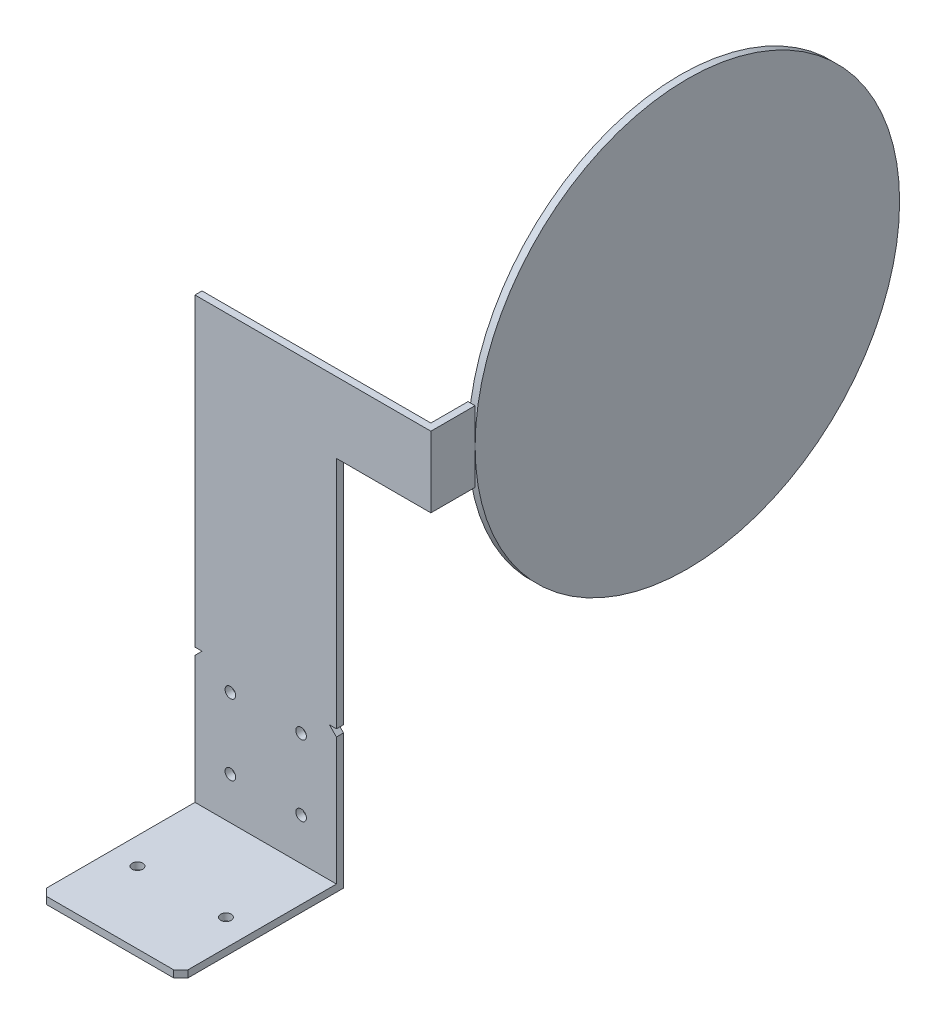
SolidWorks part; units mm, degrees
other "Markup1"
sketch "Sketch7" plane through (0, -72, -122) normal (-0.0435, -0.7938, -0.6066) x (-0.1684, -0.5927, 0.7876)
other "Markup2"
sketch "Sketch8" plane through (0, -72, -122) normal (-0.0435, -0.7938, -0.6066) x (-0.1684, -0.5927, 0.7876)
ref_plane "Спереди" through (0, 0, 0) normal (0, 0, 1) x (1, 0, 0)
ref_plane "Сверху" through (0, 0, 0) normal (0, 1, 0) x (1, 0, 0)
ref_plane "Справа" through (0, 0, 0) normal (1, 0, 0) x (0, 0, -1)
sketch "Sketch1" plane through (0, 0, 0) normal (1, 0, 0) x (0, 0, -1)
  line L0 (0, 0) -> (0, 38)
  line L1 (0, 38) -> (2, 38)
  line L2 (2, 38) -> (2, -2)
  line L3 (2, -2) -> (-44, -2)
  line L4 (-44, -2) -> (-44, 0)
  line L5 (-44, 0) -> (0, 0)
  dimension "D1" = 2
  dimension "D2" = 2
  dimension "D3" = 46
  dimension "D4" = 40
extrude "Extrude1" add sketch "Sketch1" along normal blind 40
sketch "Sketch2" plane through (0, -2, 0) normal (0, -1, 0) x (-1, 0, 0)
  line L0 (-40, 2) -> (0, 2) construction
  line L1 (-7.5, -23.75) -> (-32.5, -23.75) construction
  line L2 (-40, -44) -> (0, -44) construction
  circle A0 centre (-32.5, -23.75) radius 1.5
  circle A1 centre (-7.5, -23.75) radius 1.5
  point P5 (-20, -23.75)
  point P10 (-20, -44)
  dimension "D1" = 3
  dimension "D2" = 25
  dimension "D3" = 25.75
extrude "Extrude2" cut sketch "Sketch2" against normal up to next contours A0
sketch "Sketch3" plane through (0, 0, -2) normal (0, 0, -1) x (-1, 0, 0)
  line L1 (0, -2) -> (0, 38) construction
  line L2 (-40, 38) -> (0, 38) construction
  circle A0 centre (-10, 31.9) radius 1.5
  circle A1 centre (-30, 31.9) radius 1.5
  circle A2 centre (-30, 11.9) radius 1.5
  circle A3 centre (-10, 11.9) radius 1.5
  dimension "D1" = 10
  dimension "D2" = 6.1
  dimension "D3" = 2
  dimension "D4" = 2
extrude "Extrude3" cut sketch "Sketch3" against normal up to next
chamfer "Chamfer1" distance 2 angle 45 4 edges at (40, -1, 44) (0, -1, 44) (0, 38, -1) (40, 38, -1)
sketch "Sketch9" plane through (0, 0, -2) normal (0, 0, -1) x (-1, 0, 0)
  line L0 (-38, 38) -> (-2, 38) construction
  line L1 (0, 38) -> (-40, 38)
  line L2 (0, 38) -> (0, 124.21)
  line L3 (0, 124.21) -> (-40, 124.21)
  line L4 (-40, 38) -> (-40, 124.21)
  line L5 (-40, -2) -> (-40, 36) construction
  line L6 (0, -2) -> (0, 36) construction
  line L7 (-30, 31.9) -> (-10, 11.9) construction
  line L8 (-10, 31.9) -> (-30, 11.9) construction
  point P18 (-20, 21.9)
  dimension "D1" = 102.31
extrude "Boss-Extrude1" add sketch "Sketch9" against normal blind 2
sketch "Sketch11" plane through (0, 0, -2) normal (0, 0, -1) x (-1, 0, 0)
  line L1 (-40, 124.21) -> (-66.69, 124.21)
  line L2 (-40, 124.21) -> (-40, 104.21)
  line L3 (-40, 104.21) -> (-66.69, 104.21)
  line L4 (-66.69, 124.21) -> (-66.69, 104.21)
  dimension "D1" = 26.69
  dimension "D2" = 20
extrude "Boss-Extrude2" add sketch "Sketch11" against normal blind 2
sketch "Sketch13" plane through (66.69, 0, 0) normal (1, 0, 0) x (0, 0, -1)
  line L0 (0, 124.21) -> (0, 104.21) construction
  line L1 (2, 124.21) -> (12.5, 124.21)
  line L2 (2, 124.21) -> (2, 104.21)
  line L3 (2, 104.21) -> (12.5, 104.21)
  line L4 (12.5, 124.21) -> (12.5, 104.21)
  line L5 (0, 104.21) -> (2, 104.21) construction
  dimension "D1" = 12.5
extrude "Boss-Extrude3" add sketch "Sketch13" against normal blind 2
sketch "Sketch14" plane through (66.69, 0, 0) normal (1, 0, 0) x (0, 0, -1)
  line L0 (12.5, 104.21) -> (12.5, 124.21) construction
  circle A0 centre (72.5, 114.21) radius 60
  point P4 (12.5, 114.21)
  point P5 (0, 0)
  dimension "D1" = 120
extrude "Boss-Extrude4" add sketch "Sketch14" against normal blind 2 separate body
